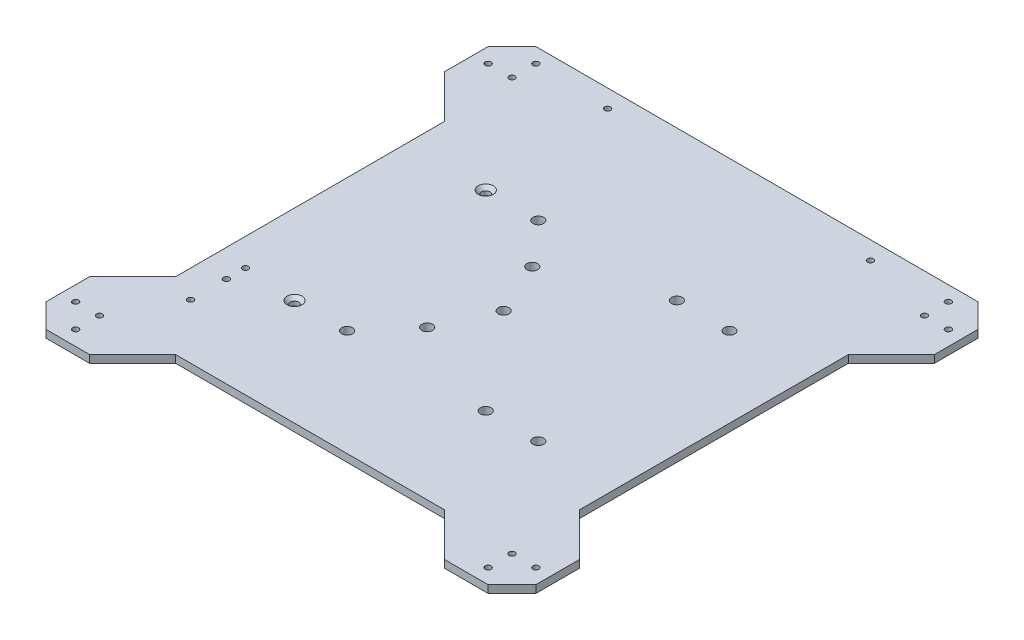
SolidWorks part; units mm, degrees
material "6061-T6 (SS)"
ref_plane "Front Plane" through (0, 0, 0) normal (0, 0, 1) x (1, 0, 0)
ref_plane "Top Plane" through (0, 0, 0) normal (0, 1, 0) x (1, 0, 0)
ref_plane "Right Plane" through (0, 0, 0) normal (1, 0, 0) x (0, 0, -1)
sketch "Sketch1" plane through (0, 0, 0) normal (0, 1, 0) x (1, 0, 0)
  line L0 (-102.5, 102.5) -> (102.5, -102.5) construction
  line L1 (-92.5, 102.5) -> (92.5, 102.5)
  line L2 (-102.5, 92.5) -> (-102.5, -92.5)
  line L3 (-92.5, -102.5) -> (92.5, -102.5)
  line L4 (102.5, 92.5) -> (102.5, -92.5)
  line L5 (92.5, -102.5) -> (102.5, -92.5)
  line L6 (92.5, 102.5) -> (102.5, 92.5)
  line L7 (-102.5, 92.5) -> (-92.5, 102.5)
  line L8 (-102.5, -92.5) -> (-92.5, -102.5)
  point P2 (-102.5, -102.5)
  point P3 (102.5, 102.5)
  dimension "D1" = 205
  dimension "D2" = 205
extrude "Boss-Extrude1" add sketch "Sketch1" along normal blind 3.175
sketch "Sketch2" plane through (0, 3.175, 0) normal (0, 1, 0) x (1, 0, 0)
  circle A0 centre (-51, -40) radius 1.5
  circle A2 centre (-29, -40) radius 2.25
  circle A5 centre (-51, 40) radius 1.5
  circle A6 centre (-29, 40) radius 2.25
  circle A9 centre (29, 40) radius 2.25
  circle A10 centre (51, 40) radius 2.25
  circle A14 centre (29, -40) radius 2.25
  circle A15 centre (51, -40) radius 2.25
  circle A16 centre (-3.5, 0) radius 2.25
  circle A17 centre (-13.5, 22) radius 2.25
  circle A18 centre (-13.5, -22) radius 2.25
  dimension "D1" = 3
  dimension "D2" = 4.5
extrude "Cut-Extrude1" cut sketch "Sketch2" against normal through all
hole_wizard "M3x0.5 Tapped Hole1" positions "Sketch4" profile "Sketch3" tap size "M3x0.5" standard "Ansi Metric" end condition through all
sketch "Sketch4" plane through (0, 3.175, 0) normal (0, 1, 0) x (-1, 0, 0)
  line L0 (92.5, 102.5) -> (-92.5, 102.5) construction
  line L1 (102.5, -92.5) -> (102.5, 92.5) construction
  line L2 (-92.5, -102.5) -> (92.5, -102.5) construction
  line L3 (-102.5, 92.5) -> (-102.5, -92.5) construction
  point P0 (96.3, -86.3)
  point P1 (86.3, -96.3)
  point P3 (-86.3, -96.3)
  point P5 (-96.3, -86.3)
  point P7 (-96.3, 86.3)
  point P9 (-86.3, 96.3)
  point P11 (86.3, 96.3)
  point P13 (96.3, 86.3)
  point P32 (-86.3, 86.3)
  point P34 (-86.3, -86.3)
  point P36 (86.3, -86.3)
  point P38 (86.3, 86.3)
  dimension "D1" = 16.2
  dimension "D2" = 6.2
  dimension "D3" = 6.2
  dimension "D4" = 16.2
  dimension "D5" = 16.2
  dimension "D6" = 6.2
  dimension "D7" = 6.2
  dimension "D8" = 16.2
sketch "Sketch3" plane through (-96.3, 3.175, -86.3) normal (1, 0, 0) x (0, 0, 1)
  line L0 (0, 0) -> (0, 3.175)
  line L1 (0, 3.175) -> (1.25, 3.175)
  line L2 (1.25, 3.175) -> (1.25, 0)
  line L5 (1.25, 0) -> (0, 0)
  line L11 (0, -6.35) -> (0, 107.95) construction
  dimension "Thru Tap Drill Dia." = 2.5
  dimension "Thru Tap Drill Depth" = 3.175
cosmetic thread "Hole Thread1" parameters "D2"=3
cosmetic thread "Hole Thread2" parameters "D2"=3
cosmetic thread "Hole Thread3" parameters "D2"=3
cosmetic thread "Hole Thread4" parameters "D2"=3
cosmetic thread "Hole Thread5" parameters "D2"=3
cosmetic thread "Hole Thread6" parameters "D2"=3
cosmetic thread "Hole Thread7" parameters "D2"=3
cosmetic thread "Hole Thread8" parameters "D2"=3
cosmetic thread "Hole Thread9" parameters "D2"=3
cosmetic thread "Hole Thread10" parameters "D2"=3
cosmetic thread "Hole Thread11" parameters "D2"=3
cosmetic thread "Hole Thread12" parameters "D2"=3
sketch "Sketch5" plane through (0, 3.175, 0) normal (0, 1, 0) x (1, 0, 0)
  circle A0 centre (-55, 95) radius 1.25
  circle A1 centre (55, 95) radius 1.25
  circle A2 centre (-55, -95) radius 1.25
  circle A3 centre (55, -95) radius 1.25
  dimension "D1" = 2.5
extrude "Cut-Extrude2" cut sketch "Sketch5" against normal through all
sketch "Sketch6" plane through (0, 3.175, 0) normal (0, 1, 0) x (1, 0, 0)
  line L0 (-92.5, -102.5) -> (92.5, -102.5) construction
  line L1 (-102.5, 92.5) -> (-102.5, -92.5) construction
  circle A0 centre (-73, -46.5) radius 1.25
  circle A1 centre (-73, -38.5) radius 1.25
  circle A2 centre (-73, -61.5) radius 1.25
  dimension "D3" = 2.5
  dimension "D1" = 56
  dimension "D2" = 29.5
  dimension "D4" = 8
  dimension "D5" = 15
extrude "Cut-Extrude3" cut sketch "Sketch6" against normal blind 10
hole_wizard "CSK for M3 Flat Head Machine Screw1" positions "Sketch8" profile "Sketch7" countersink size "M3" standard "Ansi Metric" end condition through all
sketch "Sketch8" plane through (0, 3.175, 0) normal (0, 1, 0) x (-1, 0, 0)
  point P0 (51, -40)
  point P1 (51, 40)
sketch "Sketch7" plane through (-51, 3.175, -40) normal (1, 0, 0) x (0, 0, 1)
  line L0 (0, 0) -> (0, 3.175)
  line L1 (0, 3.175) -> (1.7, 3.175)
  line L2 (1.7, 3.175) -> (1.7, 1.45)
  line L3 (1.7, 1.45) -> (3.15, 0)
  line L5 (3.15, 0) -> (0, 0)
  line L6 (-1.7, 1.45) -> (-3.15, 0) construction
  line L11 (0, -6.35) -> (0, 107.95) construction
  dimension "Thru Hole Dia." = 3.4
  dimension "Thru Hole Depth" = 3.175
  dimension "Near C'Sink Dia." = 6.3
  dimension "Near C'Sink Angle" = 90
sketch "Sketch9" plane through (0, 3.175, 0) normal (0, 1, 0) x (1, 0, 0)
  line L0 (-102.5, 74.2157) -> (-84.5, 56.2157)
  line L1 (-102.5, 92.5) -> (-102.5, -92.5) construction
  line L2 (-84.5, 56.2157) -> (-84.5, -56.2157)
  line L3 (-84.5, -56.2157) -> (-102.5, -74.2157)
  line L4 (-102.5, 74.2157) -> (-102.5, -74.2157)
  line L5 (102.5, 74.2157) -> (84.5, 56.2157)
  line L6 (102.5, -92.5) -> (102.5, 92.5) construction
  line L7 (84.5, 56.2157) -> (84.5, -56.2157)
  line L8 (84.5, -56.2157) -> (102.5, -74.2157)
  line L9 (102.5, -74.2157) -> (102.5, 74.2157)
  line L10 (-74.2157, -102.5) -> (-56.2157, -84.5)
  line L11 (-92.5, -102.5) -> (92.5, -102.5) construction
  line L12 (-56.2157, -84.5) -> (56.2157, -84.5)
  line L13 (56.2157, -84.5) -> (74.2157, -102.5)
  line L14 (74.2157, -102.5) -> (-74.2157, -102.5)
  line L16 (92.5, 102.5) -> (-92.5, 102.5) construction
  circle A0 centre (-86.3, -86.3) radius 1.25 construction
  circle A1 centre (86.3, -86.3) radius 1.25 construction
  circle A2 centre (86.3, 86.3) radius 1.25 construction
  circle A3 centre (-86.3, 86.3) radius 1.25 construction
  dimension "D6" = 20
  dimension "D1" = 45
  dimension "D2" = 18
  dimension "D3" = 18
  dimension "D4" = 18
  dimension "D5" = 20
  dimension "D7" = 20
  dimension "D8" = 20
  dimension "D9" = 20
  dimension "D10" = 20
extrude "Cut-Extrude4" cut sketch "Sketch9" against normal blind 10
